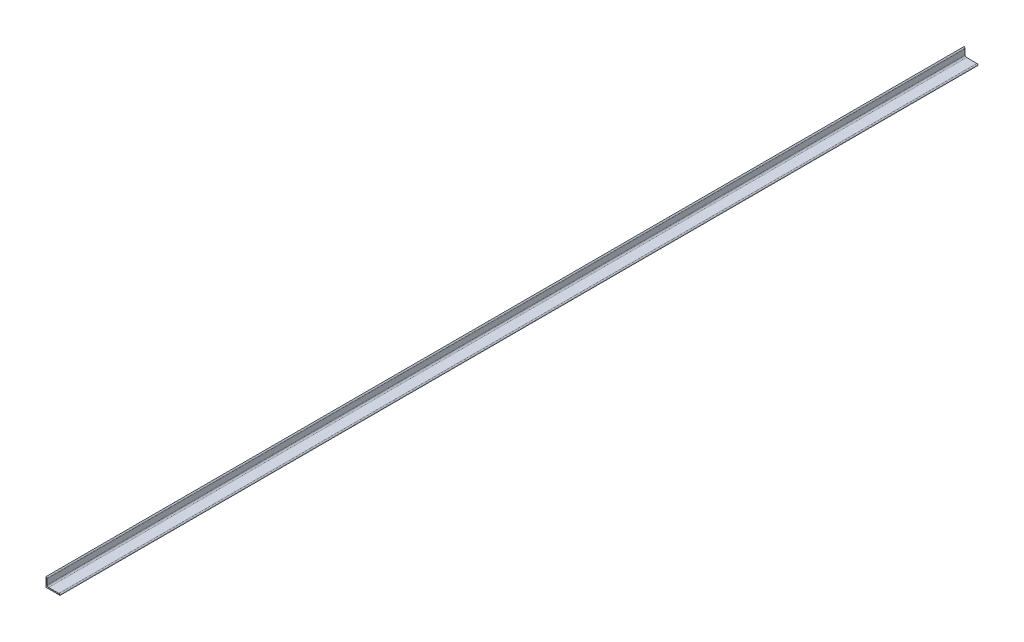
SolidWorks part; units mm, degrees
ref_plane "Plano frontal" through (0, 0, 0) normal (0, 0, 1) x (1, 0, 0)
ref_plane "Plano superior" through (0, 0, 0) normal (0, 1, 0) x (1, 0, 0)
ref_plane "Plano direito" through (0, 0, 0) normal (1, 0, 0) x (0, 0, -1)
sketch "Esboço1" plane through (0, 0, 0) normal (1, 0, 0) x (0, 0, -1)
  line L0 (0, 0) -> (5000, 0)
  dimension "D1" = 5000
other "Componente estrutural1"
ref_plane "Plano1" through (0, 0, 0) normal (0, 0, -1) x (0, 1, 0)
sketch "Sketch11" plane through (0, 0, 0) normal (0, 0, -1) x (0, 1, 0)
  line L0 (0, 0) -> (0, 76.2)
  line L1 (0, 76.2) -> (0.0051, 76.2)
  line L2 (6.35, 69.8551) -> (6.35, 14.2875)
  line L3 (14.2875, 6.35) -> (44.4551, 6.35)
  line L4 (50.8, 0.0051) -> (50.8, 0)
  line L5 (50.8, 0) -> (0, 0)
  arc A0 (50.8, 0.0051) -> (44.4551, 6.35) centre (44.4551, 0.0051) ccw
  arc A1 (0.0051, 76.2) -> (6.35, 69.8551) centre (0.0051, 69.8551) cw
  arc A2 (14.2875, 6.35) -> (6.35, 14.2875) centre (14.2875, 14.2875) cw
  point P10 (25.4, 0)
  point P14 (0, 38.1)
  point P15 (6.35, 38.1)
  point P16 (25.4, 6.35)
  point P17 (6.35, 76.2)
  point P18 (50.8, 6.35)
  point P19 (0, 0)
  dimension "D2" = 0.0051
  dimension "D3" = 76.2
  dimension "Radius_1" = 7.9375
  dimension "D1" = 6.35
  dimension "H_leg" = 50.8
